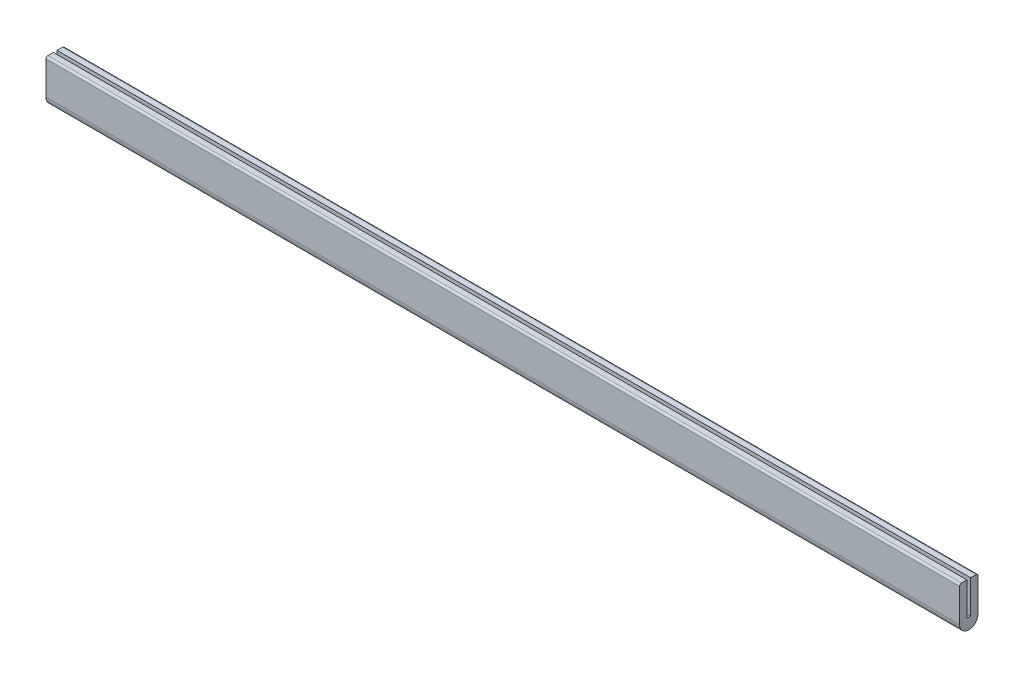
SolidWorks part; units mm, degrees
material "Rubber"
ref_plane "Front Plane" through (0, 0, 0) normal (0, 0, 1) x (1, 0, 0)
ref_plane "Top Plane" through (0, 0, 0) normal (0, 1, 0) x (1, 0, 0)
ref_plane "Right Plane" through (0, 0, 0) normal (1, 0, 0) x (0, 0, -1)
sketch "Sketch1" plane through (0, 0, 0) normal (1, 0, 0) x (0, 0, -1)
  line L0 (-1.5875, 28.575) -> (-7.9375, 28.575)
  line L1 (-1.5875, 28.575) -> (1.5875, 28.575) construction
  line L2 (-1.5875, 28.575) -> (-1.5875, 0)
  line L3 (-1.5875, 0) -> (1.5875, 0)
  line L4 (1.5875, 28.575) -> (1.5875, 0)
  line L5 (-7.9375, 28.575) -> (7.9375, 28.575) construction
  line L6 (-7.9375, 28.575) -> (-7.9375, -1.5875)
  line L8 (7.9375, 28.575) -> (7.9375, -1.5875)
  line L9 (7.9375, 28.575) -> (1.5875, 28.575)
  arc A0 (7.9375, -1.5875) -> (-7.9375, -1.5875) centre (0, -1.5875) cw
  point P4 (0, 0)
  point P10 (0, 28.575)
  point P12 (0, -9.525)
  dimension "D1" = 3.175
  dimension "D2" = 28.575
  dimension "D3" = 38.1
  dimension "D4" = 6.35
extrude "Boss-Extrude1" add sketch "Sketch1" along normal mid plane 787.4
fillet "Fillet1" radius 1.5875 2 edges at (0, 28.575, 7.9375) (0, 28.575, -7.9375)
